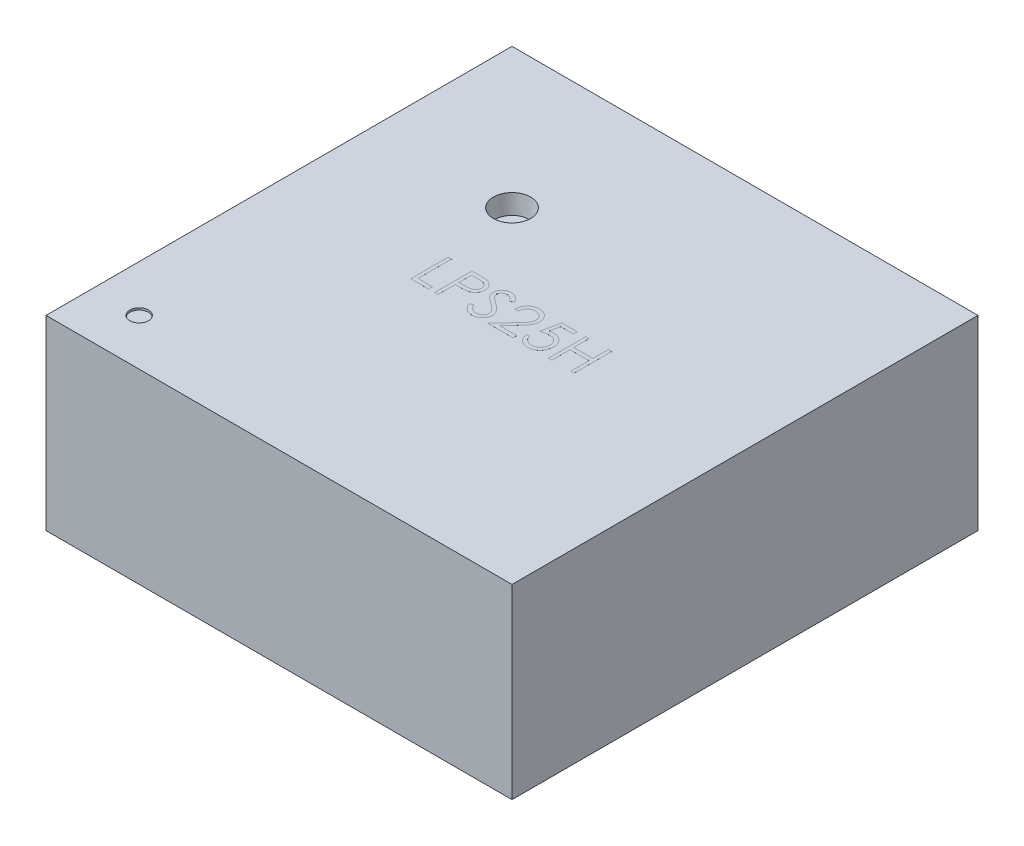
SolidWorks part; units mm, degrees
ref_plane "Front Plane" through (0, 0, 0) normal (0, 0, 1) x (1, 0, 0)
ref_plane "Top Plane" through (0, 0, 0) normal (0, 1, 0) x (1, 0, 0)
ref_plane "Right Plane" through (0, 0, 0) normal (1, 0, 0) x (0, 0, -1)
sketch "Sketch1" plane through (0, 0, 0) normal (0, 1, 0) x (1, 0, 0)
  line L1 (-1.25, -1.25) -> (1.25, -1.25)
  line L2 (-1.25, -1.25) -> (-1.25, 1.25)
  line L3 (-1.25, 1.25) -> (1.25, 1.25)
  line L4 (1.25, -1.25) -> (1.25, 1.25)
  line L5 (-1.25, -1.25) -> (1.25, 1.25) construction
  line L6 (-1.25, 1.25) -> (1.25, -1.25) construction
  point P0 (0, 0)
  dimension "D1" = 2.5
  dimension "D2" = 2.5
extrude "Boss-Extrude1" add sketch "Sketch1" along normal blind 1
sketch "Sketch2" plane through (0, 1, 0) normal (0, 1, 0) x (1, 0, 0)
  circle A0 centre (-0.5, 0.5) radius 0.1
  dimension "D1" = 0.2
  dimension "D2" = 0.5
  dimension "D3" = 0.5
extrude "Cut-Extrude1" cut sketch "Sketch2" against normal blind 0.1 draft 5
sketch "Sketch3" plane through (0, 1, 0) normal (0, 1, 0) x (1, 0, 0)
  line L0 (-1.25, -1.25) -> (1.25, -1.25) construction
  line L1 (-1.25, 1.25) -> (-1.25, -1.25) construction
  circle A0 centre (-1, -1) radius 0.05
  dimension "D1" = 0.1
  dimension "D2" = 0.25
  dimension "D3" = 0.25
extrude "Cut-Extrude2" cut sketch "Sketch3" against normal blind 0.01 draft 5
sketch "Sketch4" plane through (0, 0, 0) normal (0, -1, 0) x (1, 0, 0)
  circle A0 centre (-0.75, 1.01) radius 0.075
  dimension "D1" = 0.75
  dimension "D2" = 1.01
extrude "Cut-Extrude3" cut sketch "Sketch4" against normal blind 0.01
sketch "Sketch5" plane through (0, 0, 0) normal (0, -1, 0) x (1, 0, 0)
  line L0 (0, 1.25) -> (0, -1.25) construction
  line L1 (-1.25, 1.25) -> (1.25, 1.25) construction
  line L2 (1.25, -1.25) -> (-1.25, -1.25) construction
  line L3 (-1.25, 0) -> (1.25, 0) construction
  line L4 (-1.25, -1.25) -> (-1.25, 1.25) construction
  line L5 (1.25, 1.25) -> (1.25, -1.25) construction
  line L6 (-1.15, 0.45) -> (-1.15, 0.75)
  line L7 (-1.15, -0.15) -> (-0.7, -0.15)
  line L8 (-1.15, -0.15) -> (-1.15, 0.15)
  line L9 (-1.15, 0.15) -> (-0.7, 0.15)
  line L10 (-0.7, -0.15) -> (-0.7, 0.15)
  line L11 (-1.15, -0.15) -> (-0.7, 0.15) construction
  line L12 (-1.15, 0.15) -> (-0.7, -0.15) construction
  line L13 (-1.15, 0.75) -> (-0.7, 0.75)
  line L14 (-0.7, 0.45) -> (-0.7, 0.75)
  line L15 (-1.15, 0.45) -> (-0.7, 0.45)
  line L16 (-1.15, 0.45) -> (-0.7, 0.75) construction
  line L17 (-1.15, 0.75) -> (-0.7, 0.45) construction
  line L18 (-1.15, -0.75) -> (-0.7, -0.45) construction
  line L19 (-1.15, -0.45) -> (-0.7, -0.75) construction
  line L20 (-1.15, -0.45) -> (-0.7, -0.45)
  line L21 (-0.7, -0.45) -> (-0.7, -0.75)
  line L22 (-1.15, -0.75) -> (-0.7, -0.75)
  line L23 (-1.15, -0.45) -> (-1.15, -0.75)
  line L24 (1.15, -0.45) -> (0.7, -0.75) construction
  line L25 (1.15, -0.75) -> (0.7, -0.45) construction
  line L26 (1.15, 0.75) -> (0.7, 0.45) construction
  line L27 (1.15, 0.45) -> (0.7, 0.75) construction
  line L28 (1.15, 0.15) -> (0.7, -0.15) construction
  line L29 (1.15, -0.15) -> (0.7, 0.15) construction
  line L30 (1.15, -0.45) -> (1.15, -0.75)
  line L31 (1.15, -0.75) -> (0.7, -0.75)
  line L32 (0.7, -0.45) -> (0.7, -0.75)
  line L33 (1.15, -0.45) -> (0.7, -0.45)
  line L34 (1.15, 0.45) -> (0.7, 0.45)
  line L35 (0.7, 0.45) -> (0.7, 0.75)
  line L36 (1.15, 0.75) -> (0.7, 0.75)
  line L37 (0.7, -0.15) -> (0.7, 0.15)
  line L38 (1.15, 0.15) -> (0.7, 0.15)
  line L39 (1.15, -0.15) -> (1.15, 0.15)
  line L40 (1.15, -0.15) -> (0.7, -0.15)
  line L41 (1.15, 0.45) -> (1.15, 0.75)
  line L42 (0.45, 1.15) -> (0.15, 0.7) construction
  line L43 (-0.45, 0.7) -> (-0.15, 0.7)
  line L44 (-0.45, 0.7) -> (-0.45, 1.15)
  line L45 (-0.45, 1.15) -> (-0.15, 1.15)
  line L46 (-0.15, 0.7) -> (-0.15, 1.15)
  line L47 (-0.45, 0.7) -> (-0.15, 1.15) construction
  line L48 (-0.45, 1.15) -> (-0.15, 0.7) construction
  line L49 (0.45, 0.7) -> (0.15, 1.15) construction
  line L50 (0.15, 0.7) -> (0.15, 1.15)
  line L51 (0.45, 1.15) -> (0.15, 1.15)
  line L52 (0.45, 0.7) -> (0.45, 1.15)
  line L53 (0.45, 0.7) -> (0.15, 0.7)
  line L54 (0.45, -0.7) -> (0.15, -1.15) construction
  line L55 (-0.45, -1.15) -> (-0.15, -0.7) construction
  line L56 (-0.45, -0.7) -> (-0.15, -1.15) construction
  line L57 (0.45, -1.15) -> (0.15, -0.7) construction
  line L58 (0.45, -0.7) -> (0.15, -0.7)
  line L59 (0.45, -0.7) -> (0.45, -1.15)
  line L60 (0.45, -1.15) -> (0.15, -1.15)
  line L61 (0.15, -0.7) -> (0.15, -1.15)
  line L62 (-0.15, -0.7) -> (-0.15, -1.15)
  line L63 (-0.45, -1.15) -> (-0.15, -1.15)
  line L64 (-0.45, -0.7) -> (-0.45, -1.15)
  line L65 (-0.45, -0.7) -> (-0.15, -0.7)
  point P12 (-0.925, 0)
  point P17 (-0.925, 0.6)
  point P26 (-0.925, -0.6)
  point P39 (0.925, -0.6)
  point P40 (0.925, 0.6)
  point P41 (0.925, 0)
  point P42 (-0.3, 0.925)
  point P51 (0.3, 0.925)
  point P60 (0.3, -0.925)
  point P61 (-0.3, -0.925)
  dimension "D1" = 0.45
  dimension "D2" = 0.3
  dimension "D3" = 0.1
  dimension "D4" = 0.6
  dimension "D5" = 0.3
  dimension "D6" = 0.45
  dimension "D7" = 0.3
  dimension "D8" = 0.1
extrude "Boss-Extrude2" add sketch "Sketch5" along normal blind 0.025
sketch "Sketch6" plane through (0, 1, 0) normal (0, 1, 0) x (1, 0, 0)
  text T0 "LPS25H" font "Century Gothic" height 0.2
extrude "Boss-Extrude3" add sketch "Sketch6" along normal blind 0.0001
